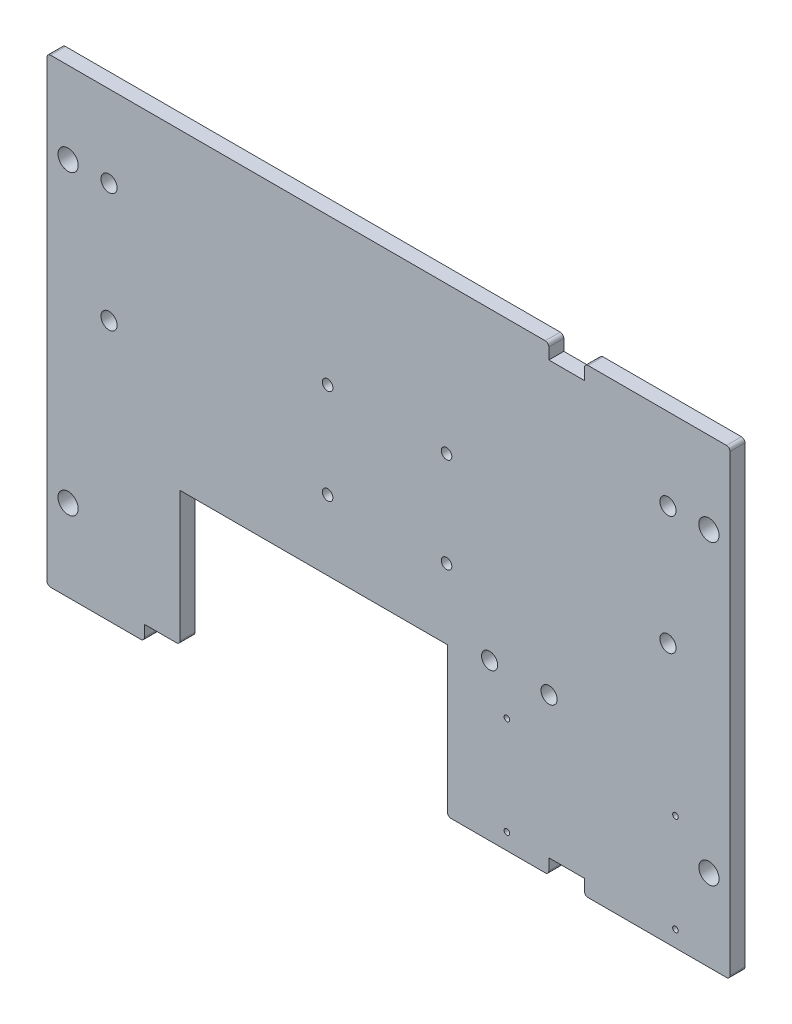
SolidWorks part; units mm, degrees
ref_plane "Front Plane" through (0, 0, 0) normal (0, 0, 1) x (1, 0, 0)
ref_plane "Top Plane" through (0, 0, 0) normal (0, 1, 0) x (1, 0, 0)
ref_plane "Right Plane" through (0, 0, 0) normal (1, 0, 0) x (0, 0, -1)
sketch "Sketch1" plane through (0, 0, 0) normal (0, 0, 1) x (1, 0, 0)
  line L1 (0, 98.425) -> (145.8854, 98.425)
  line L2 (0, 98.425) -> (0, 0)
  line L3 (0, 0) -> (145.8854, 0)
  line L4 (145.8854, 98.425) -> (145.8854, 0)
  dimension "D1" = 98.425
  dimension "D2" = 145.8854
extrude "Boss-Extrude1" add sketch "Sketch1" along normal blind 3.2004
sketch "Sketch4" plane through (0, 0, 3.2004) normal (0, 0, 1) x (1, 0, 0)
  line L0 (0, 98.425) -> (0, 0) construction
  line L1 (28.4328, 31.75) -> (85.5328, 31.75)
  line L2 (28.4328, 31.75) -> (28.4328, 0)
  line L3 (28.4328, 0) -> (85.5328, 0)
  line L4 (85.5328, 31.75) -> (85.5328, 0)
  line L5 (0, 0) -> (145.8854, 0) construction
  dimension "D1" = 28.4328
  dimension "D2" = 57.1
  dimension "D3" = 31.75
extrude "Cut-Extrude1" cut sketch "Sketch4" against normal up to surface (3.2004 mm away) up to face at (72.9427, 49.2125, 0)
sketch "Sketch5" plane through (0, 0, 3.2004) normal (0, 0, 1) x (1, 0, 0)
  line L0 (0, 49.2125) -> (4.5085, 49.2125) construction
  line L1 (4.5085, 17.4625) -> (4.5085, 80.9625) construction
  line L2 (141.3769, 49.2125) -> (145.8854, 49.2125) construction
  line L3 (141.3769, 17.4625) -> (141.3769, 80.9625) construction
  line L4 (0, 98.425) -> (0, 0) construction
  line L5 (145.8854, 0) -> (145.8854, 98.425) construction
  line L10 (72.9427, 98.425) -> (72.9427, 0) construction
  line L11 (145.8854, 98.425) -> (0, 98.425) construction
  line L12 (85.5328, 0) -> (145.8854, 0) construction
  circle A0 centre (141.3769, 80.9625) radius 2.159
  circle A1 centre (141.3769, 17.4625) radius 2.159
  circle A2 centre (4.5085, 17.4625) radius 2.159
  circle A3 centre (4.5085, 80.9625) radius 2.159
  dimension "D3" = 4.318
  dimension "D1" = 4.5085
  dimension "D2" = 63.5
extrude "Cut-Extrude2" cut sketch "Sketch5" against normal up to surface (3.2004 mm away) up to face at (64.9627, 32.5437, 0)
sketch "Sketch7" plane through (0, 0, 0) normal (0, 0, -1) x (-1, 0, 0)
  line L7 (-59.9372, 67.0177) -> (-59.9372, 46.6977) construction
  line L8 (-85.3372, 67.0177) -> (-85.3372, 46.6977) construction
  line L9 (-59.9372, 56.8577) -> (-85.3372, 56.8577) construction
  circle A10 centre (-59.9372, 67.0177) radius 1.1303
  circle A11 centre (-59.9372, 46.6977) radius 1.1303
  circle A12 centre (-85.3372, 46.6977) radius 1.1303
  circle A13 centre (-85.3372, 67.0177) radius 1.1303
  point P0 (-72.6372, 56.8577)
  point P26 (-72.6372, 56.8577)
  dimension "D6" = 2.2606
  dimension "D1" = 25.4
  dimension "D2" = 20.32
extrude "Cut-Extrude3" cut sketch "Sketch7" against normal up to surface (3.2004 mm away) up to face at (6.6675, 80.9625, 3.2004)
sketch "Sketch9" plane through (0, 0, 3.2004) normal (0, 0, 1) x (1, 0, 0)
  line L0 (110.9934, 3.175) -> (110.9934, 95.25) construction
  line L1 (114.8034, 95.25) -> (107.1834, 95.25)
  line L2 (114.8034, 95.25) -> (114.8034, 98.425)
  line L3 (114.8034, 98.425) -> (107.1834, 98.425)
  line L4 (107.1834, 95.25) -> (107.1834, 98.425)
  line L5 (114.8034, 0) -> (107.1834, 0)
  line L6 (114.8034, 0) -> (114.8034, 3.175)
  line L7 (114.8034, 3.175) -> (107.1834, 3.175)
  line L8 (107.1834, 0) -> (107.1834, 3.175)
  line L9 (28.4328, 0) -> (20.8128, 0)
  line L10 (28.4328, 0) -> (28.4328, 3.175)
  line L11 (28.4328, 3.175) -> (20.8128, 3.175)
  line L12 (145.8854, 98.425) -> (0, 98.425) construction
  line L13 (145.8854, 0) -> (145.8854, 98.425) construction
  line L14 (85.5328, 0) -> (145.8854, 0) construction
  line L15 (20.8128, 0) -> (20.8128, 3.175)
  line L16 (0, 0) -> (28.4328, 0) construction
  line L17 (28.4328, 31.75) -> (28.4328, 0) construction
  dimension "D1" = 3.175
  dimension "D2" = 34.892
  dimension "D3" = 7.62
extrude "Cut-Extrude5" cut sketch "Sketch9" against normal up to surface (3.2004 mm away) up to face at (84.2069, 67.0177, 0)
sketch "Sketch10" plane through (0, 0, 3.2004) normal (0, 0, 1) x (1, 0, 0)
  line L0 (116.2328, 0) -> (116.2328, 13.97) construction
  line L1 (134.2328, 13.97) -> (98.2328, 13.97) construction
  line L2 (98.2328, 3.47) -> (98.2328, 24.47) construction
  line L3 (134.2328, 3.47) -> (134.2328, 24.47) construction
  line L4 (114.8034, 0) -> (145.8854, 0) construction
  line L5 (85.5328, 0) -> (85.5328, 31.75) construction
  circle A4 centre (98.2328, 24.47) radius 0.5956
  circle A5 centre (134.2328, 24.47) radius 0.5956
  circle A6 centre (98.2328, 3.47) radius 0.5956
  circle A7 centre (134.2328, 3.47) radius 0.5956
  dimension "D5" = 1.1913
  dimension "D1" = 21
  dimension "D2" = 36
  dimension "D3" = 13.97
  dimension "D4" = 12.7
extrude "Cut-Extrude6" cut sketch "Sketch10" against normal up to surface (3.2004 mm away) up to face at (80.5152, 36.6889, 0)
fillet "Fillet1" radius 0.762 11 edges at (145.8854, 98.425, 1.6002) (114.8034, 98.425, 1.6002) (107.1834, 98.425, 1.6002) (0, 98.425, 1.6002) (0, 0, 1.6002) (85.5328, 0, 1.6002) (107.1834, 0, 1.6002) (114.8034, 0, 1.6002) (145.8854, 0, 1.6002) (20.8128, 0, 1.6002) (28.4328, 3.175, 1.6002)
sketch "Sketch11" plane through (0, 0, 3.2004) normal (0, 0, 1) x (1, 0, 0)
  line L0 (132.6327, 68.2625) -> (13.2527, 68.2625) construction
  line L1 (72.9427, 68.2625) -> (72.9427, 98.425) construction
  line L2 (132.6327, 55.5625) -> (132.6327, 80.9625) construction
  line L3 (13.2527, 55.5625) -> (13.2527, 80.9625) construction
  line L4 (0, 98.425) -> (145.8854, 98.425) construction
  line L5 (107.2327, 33.3375) -> (94.5327, 33.3375) construction
  line L6 (100.8827, 33.3375) -> (100.8827, 68.2625) construction
  circle A0 centre (13.2527, 55.5625) radius 1.7272
  circle A1 centre (13.2527, 80.9625) radius 1.7272
  circle A2 centre (132.6327, 55.5625) radius 1.7272
  circle A3 centre (132.6327, 80.9625) radius 1.7272
  circle A4 centre (107.2327, 33.3375) radius 1.7272
  circle A5 centre (94.5327, 33.3375) radius 1.7272
  dimension "D2" = 3.4544
  dimension "D1" = 25.4
  dimension "D3" = 119.38
  dimension "D4" = 30.1625
  dimension "D5" = 12.7
  dimension "D6" = 34.925
  dimension "D7" = 27.94
extrude "Cut-Extrude7" cut sketch "Sketch11" against normal up to surface (3.2004 mm away) up to face at (98.8284, 24.47, 0)
